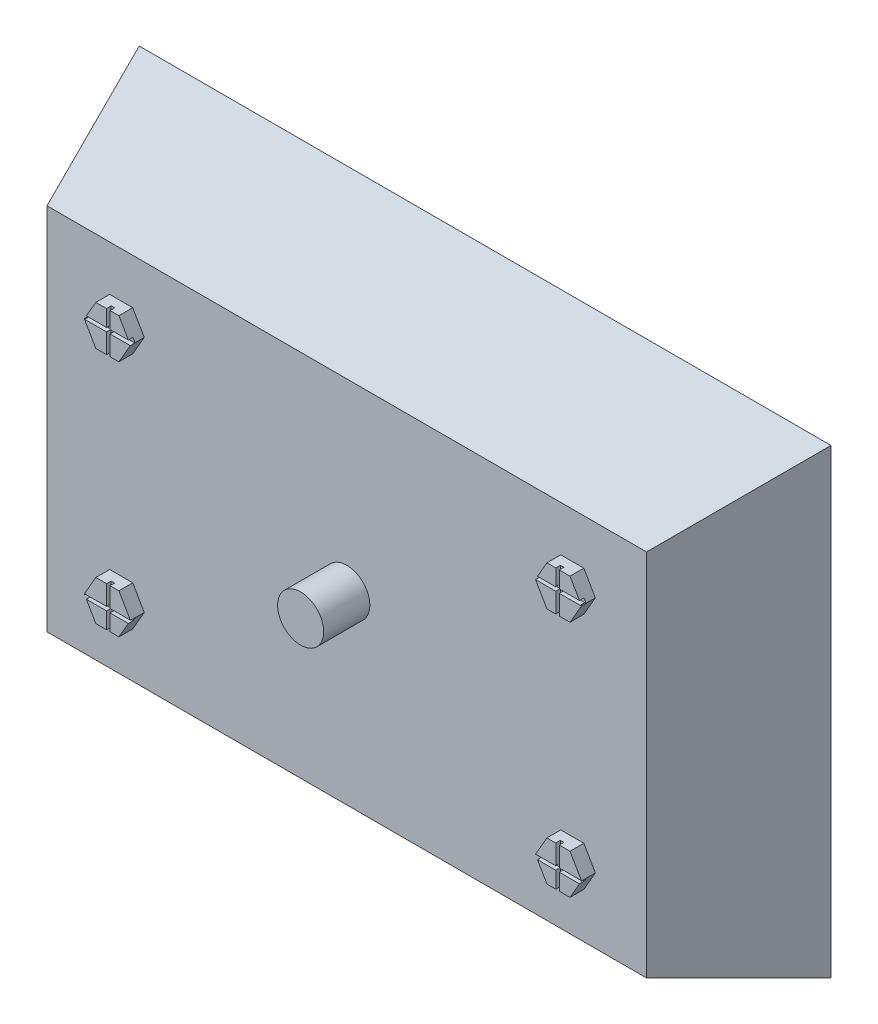
SolidWorks part; units mm, degrees
ref_plane "Front Plane" through (0, 0, 0) normal (0, 0, 1) x (1, 0, 0)
ref_plane "Top Plane" through (0, 0, 0) normal (0, 1, 0) x (1, 0, 0)
ref_plane "Right Plane" through (0, 0, 0) normal (1, 0, 0) x (0, 0, -1)
sketch "Sketch2" plane through (0, 0, 0) normal (0, 0, 1) x (1, 0, 0)
  line L1 (-75, 50) -> (75, 50)
  line L2 (-75, 50) -> (-75, -50)
  line L3 (-75, -50) -> (75, -50)
  line L4 (75, 50) -> (75, -50)
  line L5 (-75, 50) -> (75, -50) construction
  line L6 (-75, -50) -> (75, 50) construction
  point P0 (0, 0)
extrude "Boss-Extrude1" add sketch "Sketch2" against normal blind 50
chamfer "Chamfer1" distance 30 distance2 10 4 edges at (0, -50, 0) (-75, 0, 0) (0, 50, 0) (75, 0, 0)
sketch "Sketch5" plane through (75, 0, 0) normal (1, 0, 0) x (0, 0, -1)
  line L0 (30, -50) -> (30, 50)
  line L1 (30, 50) -> (81.329, 62.666)
  line L2 (81.329, 62.666) -> (65.8385, -81.9787)
  line L3 (65.8385, -81.9787) -> (30, -50)
extrude "Cut-Extrude1" cut sketch "Sketch5" against normal blind 282
sketch "Sketch6" plane through (0, 0, 0) normal (0, 0, 1) x (1, 0, 0)
  line L1 (-43.903, -25.8279) -> (-46.403, -21.4978)
  line L2 (-46.403, -21.4978) -> (-51.403, -21.4978)
  line L3 (-51.403, -21.4978) -> (-53.903, -25.8279)
  line L4 (-53.903, -25.8279) -> (-51.403, -30.158)
  line L5 (-51.403, -30.158) -> (-46.403, -30.158)
  line L6 (-46.403, -30.158) -> (-43.903, -25.8279)
  line L12 (43.903, 25.8279) -> (46.403, 21.4978)
  line L13 (46.403, 30.158) -> (43.903, 25.8279)
  line L14 (51.403, 30.158) -> (46.403, 30.158)
  line L15 (53.903, 25.8279) -> (51.403, 30.158)
  line L16 (51.403, 21.4978) -> (53.903, 25.8279)
  line L17 (46.403, 21.4978) -> (51.403, 21.4978)
  line L24 (92.806, 51.6558) -> (95.306, 47.3257) [skipped]
  line L25 (95.306, 55.986) -> (92.806, 51.6558) [skipped]
  line L26 (100.306, 55.986) -> (95.306, 55.986) [skipped]
  line L27 (102.806, 51.6558) -> (100.306, 55.986) [skipped]
  line L28 (100.306, 47.3257) -> (102.806, 51.6558) [skipped]
  line L29 (95.306, 47.3257) -> (100.306, 47.3257) [skipped]
  line L30 (-5, 0) -> (-2.5, -4.3301) [skipped]
  line L31 (-2.5, 4.3301) -> (-5, 0) [skipped]
  line L32 (2.5, 4.3301) -> (-2.5, 4.3301) [skipped]
  line L33 (5, 0) -> (2.5, 4.3301) [skipped]
  line L34 (2.5, -4.3301) -> (5, 0) [skipped]
  line L35 (-2.5, -4.3301) -> (2.5, -4.3301) [skipped]
  line L38 (46.403, -30.158) -> (43.903, -25.8279)
  line L39 (51.403, -30.158) -> (46.403, -30.158)
  line L40 (53.903, -25.8279) -> (51.403, -30.158)
  line L41 (51.403, -21.4978) -> (53.903, -25.8279)
  line L42 (46.403, -21.4978) -> (51.403, -21.4978)
  line L43 (43.903, -25.8279) -> (46.403, -21.4978)
  line L44 (-46.403, 21.4978) -> (-51.403, 21.4978)
  line L45 (-51.403, 21.4978) -> (-53.903, 25.8279)
  line L46 (-53.903, 25.8279) -> (-51.403, 30.158)
  line L47 (-51.403, 30.158) -> (-46.403, 30.158)
  line L48 (-46.403, 30.158) -> (-43.903, 25.8279)
  line L49 (-43.903, 25.8279) -> (-46.403, 21.4978)
  dimension "D1" = 4
extrude "Boss-Extrude2" add sketch "Sketch6" along normal blind 3
sketch "Sketch7" plane through (0, 0, 3) normal (0, 0, 1) x (1, 0, 0)
  line L1 (-49.075, -20.8741) -> (-48.3157, -20.8741)
  line L2 (-49.075, -20.8741) -> (-49.075, -25.7769)
  line L3 (-49.075, -31.5044) -> (-48.3157, -31.5044)
  line L4 (-48.3157, -20.8741) -> (-48.3157, -25.7769)
  line L6 (48.3157, -26.6016) -> (48.3157, -31.5044)
  line L7 (-53.8143, -25.7769) -> (-49.075, -25.7769)
  line L8 (-53.8143, -25.7769) -> (-53.8143, -26.6016)
  line L9 (-53.8143, -26.6016) -> (-49.075, -26.6016)
  line L10 (-43.5764, -25.7769) -> (-43.5764, -26.6016)
  line L13 (-48.7248, -25.7769) -> (-48.6659, -25.7769)
  line L16 (-48.7248, -26.6016) -> (-48.6659, -26.6016)
  line L17 (-48.3157, -26.6016) -> (-43.5764, -26.6016)
  line L18 (-48.3157, -25.7769) -> (-43.5764, -25.7769)
  line L19 (-49.075, -26.6016) -> (-49.075, -31.5044)
  line L20 (-48.3157, -26.6016) -> (-48.3157, -31.5044)
  line L21 (49.075, -26.6016) -> (49.075, -31.5044)
  line L22 (48.3157, -25.7769) -> (43.5764, -25.7769)
  line L23 (48.3157, -26.6016) -> (43.5764, -26.6016)
  line L24 (48.7248, -26.6016) -> (48.6659, -26.6016)
  line L25 (48.7248, -25.7769) -> (48.6659, -25.7769)
  line L26 (43.5764, -25.7769) -> (43.5764, -26.6016)
  line L27 (53.8143, -26.6016) -> (49.075, -26.6016)
  line L28 (53.8143, -25.7769) -> (53.8143, -26.6016)
  line L29 (53.8143, -25.7769) -> (49.075, -25.7769)
  line L30 (48.3157, -20.8741) -> (48.3157, -25.7769)
  line L31 (49.075, -31.5044) -> (48.3157, -31.5044)
  line L32 (49.075, -20.8741) -> (49.075, -25.7769)
  line L33 (49.075, -20.8741) -> (48.3157, -20.8741)
  line L34 (-48.3157, 26.6016) -> (-48.3157, 31.5044)
  line L35 (-49.075, 26.6016) -> (-49.075, 31.5044)
  line L36 (-48.3157, 25.7769) -> (-43.5764, 25.7769)
  line L37 (-48.3157, 26.6016) -> (-43.5764, 26.6016)
  line L38 (-48.7248, 26.6016) -> (-48.6659, 26.6016)
  line L39 (-48.7248, 25.7769) -> (-48.6659, 25.7769)
  line L40 (-43.5764, 25.7769) -> (-43.5764, 26.6016)
  line L41 (-53.8143, 26.6016) -> (-49.075, 26.6016)
  line L42 (-53.8143, 25.7769) -> (-53.8143, 26.6016)
  line L43 (-53.8143, 25.7769) -> (-49.075, 25.7769)
  line L44 (-48.3157, 20.8741) -> (-48.3157, 25.7769)
  line L45 (-49.075, 31.5044) -> (-48.3157, 31.5044)
  line L46 (-49.075, 20.8741) -> (-49.075, 25.7769)
  line L47 (-49.075, 20.8741) -> (-48.3157, 20.8741)
  line L48 (49.075, 20.8741) -> (48.3157, 20.8741)
  line L49 (49.075, 20.8741) -> (49.075, 25.7769)
  line L50 (49.075, 31.5044) -> (48.3157, 31.5044)
  line L51 (48.3157, 20.8741) -> (48.3157, 25.7769)
  line L52 (53.8143, 25.7769) -> (49.075, 25.7769)
  line L53 (53.8143, 25.7769) -> (53.8143, 26.6016)
  line L54 (53.8143, 26.6016) -> (49.075, 26.6016)
  line L55 (43.5764, 25.7769) -> (43.5764, 26.6016)
  line L56 (48.7248, 25.7769) -> (48.6659, 25.7769)
  line L57 (48.7248, 26.6016) -> (48.6659, 26.6016)
  line L58 (48.3157, 26.6016) -> (43.5764, 26.6016)
  line L59 (48.3157, 25.7769) -> (43.5764, 25.7769)
  line L60 (49.075, 26.6016) -> (49.075, 31.5044)
  line L61 (48.3157, 26.6016) -> (48.3157, 31.5044)
  point P0 (-48.6953, -26.1893)
  point P5 (-48.6953, -26.1893)
  point P38 (48.6953, -26.1893)
  point P55 (-48.6953, 26.1893)
  point P72 (48.6953, 26.1893)
extrude "Cut-Extrude2" cut sketch "Sketch7" against normal blind 1
sketch "Sketch9" plane through (0, 0, 0) normal (0, 0, 1) x (1, 0, 0)
  circle A0 centre (0, 0) radius 5
extrude "Boss-Extrude3" add sketch "Sketch9" along normal blind 10
